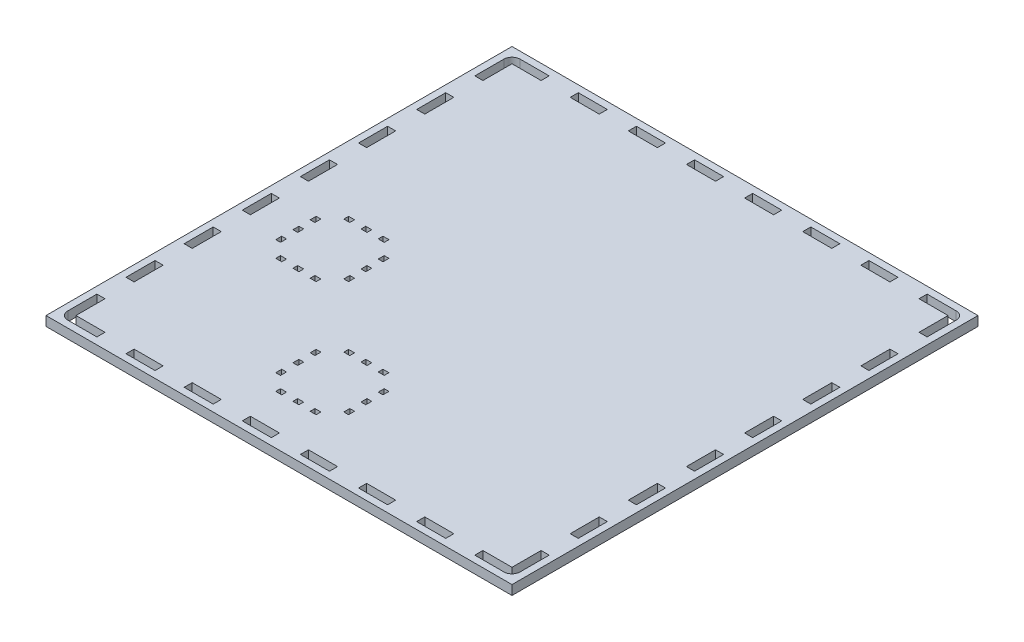
SolidWorks part; units mm, degrees
ref_plane "Front Plane" through (0, 0, 0) normal (0, 0, 1) x (1, 0, 0)
ref_plane "Top Plane" through (0, 0, 0) normal (0, 1, 0) x (1, 0, 0)
ref_plane "Right Plane" through (0, 0, 0) normal (1, 0, 0) x (0, 0, -1)
sketch "Sketch1" plane through (0, 0, 0) normal (0, 1, 0) x (1, 0, 0)
  line L182 (-7.5125, 303.9125) -> (303.8875, 303.9125)
  line L183 (-7.5125, 303.9125) -> (-7.5125, -7.4875)
  line L184 (-7.5125, -7.4875) -> (303.8875, -7.4875)
  line L185 (303.8875, 303.9125) -> (303.8875, -7.4875)
  line L195 (-2.9125, 60.7875) -> (2.4875, 60.7875)
  line L196 (-2.9125, 60.7875) -> (-2.9125, 41.3625)
  line L197 (-2.9125, 41.3625) -> (2.4875, 41.3625)
  line L198 (2.4875, 60.7875) -> (2.4875, 41.3625)
  line L200 (-2.9125, 99.6375) -> (2.4875, 99.6375)
  line L201 (-2.9125, 99.6375) -> (-2.9125, 80.2125)
  line L202 (-2.9125, 80.2125) -> (2.4875, 80.2125)
  line L203 (2.4875, 99.6375) -> (2.4875, 80.2125)
  line L205 (-2.9125, 138.4875) -> (2.4875, 138.4875)
  line L206 (-2.9125, 138.4875) -> (-2.9125, 119.0625)
  line L207 (-2.9125, 119.0625) -> (2.4875, 119.0625)
  line L208 (2.4875, 138.4875) -> (2.4875, 119.0625)
  line L211 (-2.9125, 177.3375) -> (2.4875, 177.3375)
  line L212 (-2.9125, 177.3375) -> (-2.9125, 157.9125)
  line L213 (-2.9125, 157.9125) -> (2.4875, 157.9125)
  line L214 (2.4875, 177.3375) -> (2.4875, 157.9125)
  line L216 (-2.9125, 216.1875) -> (2.4875, 216.1875)
  line L217 (-2.9125, 216.1875) -> (-2.9125, 196.7625)
  line L218 (-2.9125, 196.7625) -> (2.4875, 196.7625)
  line L219 (2.4875, 216.1875) -> (2.4875, 196.7625)
  line L221 (-2.9125, 255.0375) -> (2.4875, 255.0375)
  line L222 (-2.9125, 255.0375) -> (-2.9125, 235.6125)
  line L223 (-2.9125, 235.6125) -> (2.4875, 235.6125)
  line L224 (2.4875, 255.0375) -> (2.4875, 235.6125)
  line L236 (41.3625, 299.3125) -> (60.7875, 299.3125)
  line L237 (41.3625, 299.3125) -> (41.3625, 293.9125)
  line L238 (41.3625, 293.9125) -> (60.7875, 293.9125)
  line L239 (60.7875, 299.3125) -> (60.7875, 293.9125)
  line L241 (80.2125, 299.3125) -> (99.6375, 299.3125)
  line L242 (80.2125, 299.3125) -> (80.2125, 293.9125)
  line L243 (80.2125, 293.9125) -> (99.6375, 293.9125)
  line L244 (99.6375, 299.3125) -> (99.6375, 293.9125)
  line L246 (119.0625, 299.3125) -> (138.4875, 299.3125)
  line L247 (119.0625, 299.3125) -> (119.0625, 293.9125)
  line L248 (119.0625, 293.9125) -> (138.4875, 293.9125)
  line L249 (138.4875, 299.3125) -> (138.4875, 293.9125)
  line L251 (157.9125, 299.3125) -> (177.3375, 299.3125)
  line L252 (157.9125, 299.3125) -> (157.9125, 293.9125)
  line L253 (157.9125, 293.9125) -> (177.3375, 293.9125)
  line L254 (177.3375, 299.3125) -> (177.3375, 293.9125)
  line L256 (196.7625, 299.3125) -> (216.1875, 299.3125)
  line L257 (196.7625, 299.3125) -> (196.7625, 293.9125)
  line L258 (196.7625, 293.9125) -> (216.1875, 293.9125)
  line L259 (216.1875, 299.3125) -> (216.1875, 293.9125)
  line L260 (235.6125, 299.3125) -> (255.0375, 299.3125)
  line L261 (235.6125, 299.3125) -> (235.6125, 293.9125)
  line L262 (235.6125, 293.9125) -> (255.0375, 293.9125)
  line L263 (255.0375, 299.3125) -> (255.0375, 293.9125)
  line L272 (299.2875, 255.0625) -> (293.8875, 255.0625)
  line L273 (299.2875, 255.0625) -> (299.2875, 235.6375)
  line L274 (299.2875, 235.6375) -> (293.8875, 235.6375)
  line L275 (293.8875, 255.0625) -> (293.8875, 235.6375)
  line L276 (299.2875, 216.2125) -> (293.8875, 216.2125)
  line L277 (299.2875, 216.2125) -> (299.2875, 196.7875)
  line L278 (299.2875, 196.7875) -> (293.8875, 196.7875)
  line L279 (293.8875, 216.2125) -> (293.8875, 196.7875)
  line L280 (299.2875, 177.3625) -> (293.8875, 177.3625)
  line L281 (299.2875, 177.3625) -> (299.2875, 157.9375)
  line L282 (299.2875, 157.9375) -> (293.8875, 157.9375)
  line L283 (293.8875, 177.3625) -> (293.8875, 157.9375)
  line L284 (299.2875, 138.5125) -> (293.8875, 138.5125)
  line L285 (299.2875, 138.5125) -> (299.2875, 119.0875)
  line L286 (299.2875, 119.0875) -> (293.8875, 119.0875)
  line L287 (293.8875, 138.5125) -> (293.8875, 119.0875)
  line L288 (299.2875, 99.6625) -> (293.8875, 99.6625)
  line L289 (299.2875, 99.6625) -> (299.2875, 80.2375)
  line L290 (299.2875, 80.2375) -> (293.8875, 80.2375)
  line L291 (293.8875, 99.6625) -> (293.8875, 80.2375)
  line L292 (299.2875, 60.8125) -> (293.8875, 60.8125)
  line L293 (299.2875, 60.8125) -> (299.2875, 41.3875)
  line L294 (299.2875, 41.3875) -> (293.8875, 41.3875)
  line L295 (293.8875, 60.8125) -> (293.8875, 41.3875)
  line L304 (255.0125, 2.5125) -> (235.5875, 2.5125)
  line L305 (255.0125, 2.5125) -> (255.0125, -2.8875)
  line L306 (255.0125, -2.8875) -> (235.5875, -2.8875)
  line L307 (235.5875, 2.5125) -> (235.5875, -2.8875)
  line L308 (216.1625, 2.5125) -> (196.7375, 2.5125)
  line L309 (216.1625, 2.5125) -> (216.1625, -2.8875)
  line L310 (216.1625, -2.8875) -> (196.7375, -2.8875)
  line L311 (196.7375, 2.5125) -> (196.7375, -2.8875)
  line L312 (177.3125, 2.5125) -> (157.8875, 2.5125)
  line L313 (177.3125, 2.5125) -> (177.3125, -2.8875)
  line L314 (177.3125, -2.8875) -> (157.8875, -2.8875)
  line L315 (157.8875, 2.5125) -> (157.8875, -2.8875)
  line L316 (138.4625, 2.5125) -> (119.0375, 2.5125)
  line L317 (138.4625, 2.5125) -> (138.4625, -2.8875)
  line L318 (138.4625, -2.8875) -> (119.0375, -2.8875)
  line L319 (119.0375, 2.5125) -> (119.0375, -2.8875)
  line L320 (99.6125, 2.5125) -> (80.1875, 2.5125)
  line L321 (99.6125, 2.5125) -> (99.6125, -2.8875)
  line L322 (99.6125, -2.8875) -> (80.1875, -2.8875)
  line L323 (80.1875, 2.5125) -> (80.1875, -2.8875)
  line L324 (60.7625, 2.5125) -> (41.3375, 2.5125)
  line L325 (60.7625, 2.5125) -> (60.7625, -2.8875)
  line L326 (60.7625, -2.8875) -> (41.3375, -2.8875)
  line L327 (41.3375, 2.5125) -> (41.3375, -2.8875)
  line L528 (36.1625, 151.0125) -> (40.1625, 151.0125)
  line L529 (36.1625, 151.0125) -> (36.1625, 147.8375)
  line L530 (36.1625, 147.8375) -> (40.1625, 147.8375)
  line L531 (40.1625, 151.0125) -> (40.1625, 147.8375)
  line L532 (47.6625, 151.0125) -> (51.6625, 151.0125)
  line L533 (47.6625, 151.0125) -> (47.6625, 147.8375)
  line L534 (47.6625, 147.8375) -> (51.6625, 147.8375)
  line L535 (51.6625, 151.0125) -> (51.6625, 147.8375)
  line L536 (59.1625, 151.0125) -> (63.1625, 151.0125)
  line L537 (59.1625, 151.0125) -> (59.1625, 147.8375)
  line L538 (59.1625, 147.8375) -> (63.1625, 147.8375)
  line L539 (63.1625, 151.0125) -> (63.1625, 147.8375)
  line L540 (70.8125, 140.1875) -> (73.9875, 140.1875)
  line L541 (70.8125, 140.1875) -> (70.8125, 136.1875)
  line L542 (70.8125, 136.1875) -> (73.9875, 136.1875)
  line L543 (73.9875, 140.1875) -> (73.9875, 136.1875)
  line L544 (70.8125, 128.6875) -> (73.9875, 128.6875)
  line L545 (70.8125, 128.6875) -> (70.8125, 124.6875)
  line L546 (70.8125, 124.6875) -> (73.9875, 124.6875)
  line L547 (73.9875, 128.6875) -> (73.9875, 124.6875)
  line L548 (70.8125, 117.1875) -> (73.9875, 117.1875)
  line L549 (70.8125, 117.1875) -> (70.8125, 113.1875)
  line L550 (70.8125, 113.1875) -> (73.9875, 113.1875)
  line L551 (73.9875, 117.1875) -> (73.9875, 113.1875)
  line L552 (63.1625, 105.5375) -> (59.1625, 105.5375)
  line L553 (63.1625, 105.5375) -> (63.1625, 102.3625)
  line L554 (63.1625, 102.3625) -> (59.1625, 102.3625)
  line L555 (59.1625, 105.5375) -> (59.1625, 102.3625)
  line L556 (51.6625, 105.5375) -> (47.6625, 105.5375)
  line L557 (51.6625, 105.5375) -> (51.6625, 102.3625)
  line L558 (51.6625, 102.3625) -> (47.6625, 102.3625)
  line L559 (47.6625, 105.5375) -> (47.6625, 102.3625)
  line L560 (40.1625, 105.5375) -> (36.1625, 105.5375)
  line L561 (40.1625, 105.5375) -> (40.1625, 102.3625)
  line L562 (40.1625, 102.3625) -> (36.1625, 102.3625)
  line L563 (36.1625, 105.5375) -> (36.1625, 102.3625)
  line L564 (28.5125, 113.1875) -> (25.3375, 113.1875)
  line L565 (28.5125, 113.1875) -> (28.5125, 117.1875)
  line L566 (28.5125, 117.1875) -> (25.3375, 117.1875)
  line L567 (25.3375, 113.1875) -> (25.3375, 117.1875)
  line L568 (28.5125, 124.6875) -> (25.3375, 124.6875)
  line L569 (28.5125, 124.6875) -> (28.5125, 128.6875)
  line L570 (28.5125, 128.6875) -> (25.3375, 128.6875)
  line L571 (25.3375, 124.6875) -> (25.3375, 128.6875)
  line L572 (28.5125, 136.1875) -> (25.3375, 136.1875)
  line L573 (28.5125, 136.1875) -> (28.5125, 140.1875)
  line L574 (28.5125, 140.1875) -> (25.3375, 140.1875)
  line L575 (25.3375, 136.1875) -> (25.3375, 140.1875)
  line L576 (113.1625, 74.0125) -> (117.1625, 74.0125)
  line L577 (113.1625, 74.0125) -> (113.1625, 70.8375)
  line L578 (113.1625, 70.8375) -> (117.1625, 70.8375)
  line L579 (117.1625, 74.0125) -> (117.1625, 70.8375)
  line L580 (124.6625, 74.0125) -> (128.6625, 74.0125)
  line L581 (124.6625, 74.0125) -> (124.6625, 70.8375)
  line L582 (124.6625, 70.8375) -> (128.6625, 70.8375)
  line L583 (128.6625, 74.0125) -> (128.6625, 70.8375)
  line L584 (136.1625, 74.0125) -> (140.1625, 74.0125)
  line L585 (136.1625, 74.0125) -> (136.1625, 70.8375)
  line L586 (136.1625, 70.8375) -> (140.1625, 70.8375)
  line L587 (140.1625, 74.0125) -> (140.1625, 70.8375)
  line L588 (150.9875, 63.1875) -> (147.8125, 63.1875)
  line L589 (150.9875, 63.1875) -> (150.9875, 59.1875)
  line L590 (150.9875, 59.1875) -> (147.8125, 59.1875)
  line L591 (147.8125, 63.1875) -> (147.8125, 59.1875)
  line L592 (150.9875, 51.6875) -> (147.8125, 51.6875)
  line L593 (150.9875, 51.6875) -> (150.9875, 47.6875)
  line L594 (150.9875, 47.6875) -> (147.8125, 47.6875)
  line L595 (147.8125, 51.6875) -> (147.8125, 47.6875)
  line L596 (150.9875, 40.1875) -> (147.8125, 40.1875)
  line L597 (150.9875, 40.1875) -> (150.9875, 36.1875)
  line L598 (150.9875, 36.1875) -> (147.8125, 36.1875)
  line L599 (147.8125, 40.1875) -> (147.8125, 36.1875)
  line L600 (140.1625, 28.5375) -> (136.1625, 28.5375)
  line L601 (140.1625, 28.5375) -> (140.1625, 25.3625)
  line L602 (140.1625, 25.3625) -> (136.1625, 25.3625)
  line L603 (136.1625, 28.5375) -> (136.1625, 25.3625)
  line L604 (128.6625, 28.5375) -> (124.6625, 28.5375)
  line L605 (128.6625, 28.5375) -> (128.6625, 25.3625)
  line L606 (128.6625, 25.3625) -> (124.6625, 25.3625)
  line L607 (124.6625, 28.5375) -> (124.6625, 25.3625)
  line L608 (117.1625, 28.5375) -> (113.1625, 28.5375)
  line L609 (117.1625, 28.5375) -> (117.1625, 25.3625)
  line L610 (117.1625, 25.3625) -> (113.1625, 25.3625)
  line L611 (113.1625, 28.5375) -> (113.1625, 25.3625)
  line L612 (105.5125, 36.1875) -> (102.3375, 36.1875)
  line L613 (105.5125, 36.1875) -> (105.5125, 40.1875)
  line L614 (105.5125, 40.1875) -> (102.3375, 40.1875)
  line L615 (102.3375, 36.1875) -> (102.3375, 40.1875)
  line L616 (105.5125, 47.6875) -> (102.3375, 47.6875)
  line L617 (105.5125, 47.6875) -> (105.5125, 51.6875)
  line L618 (105.5125, 51.6875) -> (102.3375, 51.6875)
  line L619 (102.3375, 47.6875) -> (102.3375, 51.6875)
  line L620 (105.5125, 59.1875) -> (102.3375, 59.1875)
  line L621 (105.5125, 59.1875) -> (105.5125, 63.1875)
  line L622 (105.5125, 63.1875) -> (102.3375, 63.1875)
  line L623 (102.3375, 59.1875) -> (102.3375, 63.1875)
  dimension "D1" = 311.4
  dimension "D3" = 311.4
extrude "Boss-Extrude4" add sketch "Sketch1" along normal blind 6.35
sketch "Sketch4" plane through (0, 6.35, 0) normal (0, 1, 0) x (1, 0, 0)
  line L0 (303.8875, 303.9125) -> (-7.5125, 303.9125) construction
  line B0 (41.3375, 2.5125) -> (60.7625, 2.5125)
  line B1 (2.4875, 2.5125) -> (21.9125, 2.5125)
  line B2 (2.4875, 2.5125) -> (2.4875, -2.8875)
  line B3 (2.4875, -2.8875) -> (21.9125, -2.8875)
  line B4 (21.9125, 2.5125) -> (21.9125, -2.8875)
  line B5 (41.3375, 2.5125) -> (41.3375, -2.8875)
  line B6 (41.3375, -2.8875) -> (60.7625, -2.8875)
  line B7 (60.7625, 2.5125) -> (60.7625, -2.8875)
  line B8 (80.1875, 2.5125) -> (99.6125, 2.5125)
  line B9 (80.1875, 2.5125) -> (80.1875, -2.8875)
  line B10 (80.1875, -2.8875) -> (99.6125, -2.8875)
  line B11 (99.6125, 2.5125) -> (99.6125, -2.8875)
  line B12 (119.0375, 2.5125) -> (138.4625, 2.5125)
  line B13 (119.0375, 2.5125) -> (119.0375, -2.8875)
  line B14 (119.0375, -2.8875) -> (138.4625, -2.8875)
  line B15 (138.4625, 2.5125) -> (138.4625, -2.8875)
  line B16 (157.8875, 2.5125) -> (177.3125, 2.5125)
  line B17 (157.8875, 2.5125) -> (157.8875, -2.8875)
  line B18 (157.8875, -2.8875) -> (177.3125, -2.8875)
  line B19 (177.3125, 2.5125) -> (177.3125, -2.8875)
  line B20 (196.7375, 2.5125) -> (216.1625, 2.5125)
  line B21 (196.7375, 2.5125) -> (196.7375, -2.8875)
  line B22 (196.7375, -2.8875) -> (216.1625, -2.8875)
  line B23 (216.1625, 2.5125) -> (216.1625, -2.8875)
  line B24 (235.5875, 2.5125) -> (255.0125, 2.5125)
  line B25 (235.5875, 2.5125) -> (235.5875, -2.8875)
  line B26 (235.5875, -2.8875) -> (255.0125, -2.8875)
  line B27 (255.0125, 2.5125) -> (255.0125, -2.8875)
  line B28 (274.4375, 2.5125) -> (293.8625, 2.5125)
  line B29 (274.4375, 2.5125) -> (274.4375, -2.8875)
  line B30 (274.4375, -2.8875) -> (293.8625, -2.8875)
  line B31 (293.8625, 2.5125) -> (293.8625, -2.8875)
  line B32 (-2.9125, 60.7875) -> (2.4875, 60.7875)
  line B33 (-2.9125, 2.5125) -> (2.4875, 2.5125)
  line B34 (-2.9125, 2.5125) -> (-2.9125, 21.9375)
  line B35 (-2.9125, 21.9375) -> (2.4875, 21.9375)
  line B36 (2.4875, 2.5125) -> (2.4875, 21.9375)
  line B37 (2.4875, 41.3625) -> (2.4875, 60.7875)
  line B38 (-2.9125, 41.3625) -> (-2.9125, 60.7875)
  line B39 (-2.9125, 41.3625) -> (2.4875, 41.3625)
  line B40 (-2.9125, 99.6375) -> (2.4875, 99.6375)
  line B41 (2.4875, 80.2125) -> (2.4875, 99.6375)
  line B42 (-2.9125, 80.2125) -> (-2.9125, 99.6375)
  line B43 (-2.9125, 80.2125) -> (2.4875, 80.2125)
  line B44 (-2.9125, 138.4875) -> (2.4875, 138.4875)
  line B45 (2.4875, 119.0625) -> (2.4875, 138.4875)
  line B46 (-2.9125, 119.0625) -> (-2.9125, 138.4875)
  line B47 (-2.9125, 119.0625) -> (2.4875, 119.0625)
  line B48 (-2.9125, 177.3375) -> (2.4875, 177.3375)
  line B49 (2.4875, 157.9125) -> (2.4875, 177.3375)
  line B50 (-2.9125, 157.9125) -> (-2.9125, 177.3375)
  line B51 (-2.9125, 157.9125) -> (2.4875, 157.9125)
  line B52 (-2.9125, 216.1875) -> (2.4875, 216.1875)
  line B53 (2.4875, 196.7625) -> (2.4875, 216.1875)
  line B54 (-2.9125, 196.7625) -> (-2.9125, 216.1875)
  line B55 (-2.9125, 196.7625) -> (2.4875, 196.7625)
  line B56 (-2.9125, 255.0375) -> (2.4875, 255.0375)
  line B57 (2.4875, 235.6125) -> (2.4875, 255.0375)
  line B58 (-2.9125, 235.6125) -> (-2.9125, 255.0375)
  line B59 (-2.9125, 235.6125) -> (2.4875, 235.6125)
  line B60 (-2.9125, 293.8875) -> (2.4875, 293.8875)
  line B61 (2.4875, 274.4625) -> (2.4875, 293.8875)
  line B62 (-2.9125, 274.4625) -> (-2.9125, 293.8875)
  line B63 (-2.9125, 274.4625) -> (2.4875, 274.4625)
  line B64 (-7.5125, 303.9125) -> (303.8875, -7.4875) construction
  line B65 (21.9375, 299.3125) -> (21.9375, 293.9125)
  line B66 (21.9375, 299.3125) -> (2.5125, 299.3125)
  line B67 (21.9375, 293.9125) -> (2.5125, 293.9125)
  line B68 (2.5125, 299.3125) -> (2.5125, 293.9125)
  line B69 (60.7875, 299.3125) -> (60.7875, 293.9125)
  line B70 (60.7875, 299.3125) -> (41.3625, 299.3125)
  line B71 (60.7875, 293.9125) -> (41.3625, 293.9125)
  line B72 (41.3625, 299.3125) -> (41.3625, 293.9125)
  line B73 (99.6375, 299.3125) -> (99.6375, 293.9125)
  line B74 (99.6375, 299.3125) -> (80.2125, 299.3125)
  line B75 (99.6375, 293.9125) -> (80.2125, 293.9125)
  line B76 (80.2125, 299.3125) -> (80.2125, 293.9125)
  line B77 (138.4875, 299.3125) -> (138.4875, 293.9125)
  line B78 (138.4875, 299.3125) -> (119.0625, 299.3125)
  line B79 (138.4875, 293.9125) -> (119.0625, 293.9125)
  line B80 (119.0625, 299.3125) -> (119.0625, 293.9125)
  line B81 (177.3375, 299.3125) -> (177.3375, 293.9125)
  line B82 (177.3375, 299.3125) -> (157.9125, 299.3125)
  line B83 (177.3375, 293.9125) -> (157.9125, 293.9125)
  line B84 (157.9125, 299.3125) -> (157.9125, 293.9125)
  line B85 (216.1875, 299.3125) -> (216.1875, 293.9125)
  line B86 (216.1875, 299.3125) -> (196.7625, 299.3125)
  line B87 (216.1875, 293.9125) -> (196.7625, 293.9125)
  line B88 (196.7625, 299.3125) -> (196.7625, 293.9125)
  line B89 (255.0375, 299.3125) -> (255.0375, 293.9125)
  line B90 (255.0375, 299.3125) -> (235.6125, 299.3125)
  line B91 (255.0375, 293.9125) -> (235.6125, 293.9125)
  line B92 (293.8875, 293.9125) -> (274.4625, 293.9125)
  line B93 (274.4625, 299.3125) -> (274.4625, 293.9125)
  line B94 (293.8875, 299.3125) -> (274.4625, 299.3125)
  line B95 (293.8875, 299.3125) -> (293.8875, 293.9125)
  line B96 (235.6125, 299.3125) -> (235.6125, 293.9125)
  line B97 (293.8875, 2.5375) -> (299.2875, 2.5375)
  line B98 (299.2875, 21.9625) -> (299.2875, 2.5375)
  line B99 (293.8875, 21.9625) -> (299.2875, 21.9625)
  line B100 (293.8875, 21.9625) -> (293.8875, 2.5375)
  line B101 (293.8875, 41.3875) -> (299.2875, 41.3875)
  line B102 (299.2875, 60.8125) -> (299.2875, 41.3875)
  line B103 (293.8875, 60.8125) -> (299.2875, 60.8125)
  line B104 (293.8875, 60.8125) -> (293.8875, 41.3875)
  line B105 (293.8875, 80.2375) -> (299.2875, 80.2375)
  line B106 (299.2875, 99.6625) -> (299.2875, 80.2375)
  line B107 (293.8875, 99.6625) -> (299.2875, 99.6625)
  line B108 (293.8875, 99.6625) -> (293.8875, 80.2375)
  line B109 (293.8875, 119.0875) -> (299.2875, 119.0875)
  line B110 (299.2875, 138.5125) -> (299.2875, 119.0875)
  line B111 (293.8875, 138.5125) -> (299.2875, 138.5125)
  line B112 (293.8875, 138.5125) -> (293.8875, 119.0875)
  line B113 (293.8875, 157.9375) -> (299.2875, 157.9375)
  line B114 (299.2875, 177.3625) -> (299.2875, 157.9375)
  line B115 (293.8875, 177.3625) -> (299.2875, 177.3625)
  line B116 (293.8875, 177.3625) -> (293.8875, 157.9375)
  line B117 (293.8875, 196.7875) -> (299.2875, 196.7875)
  line B118 (299.2875, 216.2125) -> (299.2875, 196.7875)
  line B119 (293.8875, 216.2125) -> (299.2875, 216.2125)
  line B120 (293.8875, 216.2125) -> (293.8875, 196.7875)
  line B121 (293.8875, 235.6375) -> (299.2875, 235.6375)
  line B122 (299.2875, 255.0625) -> (299.2875, 235.6375)
  line B123 (293.8875, 255.0625) -> (299.2875, 255.0625)
  line B124 (293.8875, 274.4875) -> (299.2875, 274.4875)
  line B125 (299.2875, 293.9125) -> (299.2875, 274.4875)
  line B126 (293.8875, 293.9125) -> (299.2875, 293.9125)
  line B127 (293.8875, 293.9125) -> (293.8875, 274.4875)
  line B128 (293.8875, 255.0625) -> (293.8875, 235.6375)
  line B129 (2.5125, 293.9125) -> (2.4875, 293.8875)
  line B130 (293.8875, 2.5375) -> (293.8625, 2.5125)
  line B131 (35.6625, 260.7375) -> (115.6625, 260.7375)
  line B132 (35.6625, 260.7375) -> (35.6625, 180.7375)
  line B133 (35.6625, 180.7375) -> (115.6625, 180.7375)
  line B134 (115.6625, 260.7375) -> (115.6625, 180.7375)
  arc B135 (-2.9125, 293.8875) -> (2.5125, 299.2874) centre (2.4875, 293.8875) cw
  arc B136 (293.8625, -2.8875) -> (299.2624, 2.5375) centre (293.8625, 2.5125) ccw
  arc B137 (299.2875, 293.9125) -> (293.8875, 299.3125) centre (293.8875, 293.9125) ccw
  arc B138 (2.4875, -2.8875) -> (-2.9125, 2.5125) centre (2.4875, 2.5125) cw
sketch_block_instance "Outer Mounting Holes-4"
sketch_block "Outer Mounting Holes" parameters "D1"=5.4, "D2"=19.425, "D3"=19.425, "D4"=19.425, "D5"=80, "D6"=302.2
extrude "Cut-Extrude3" cut sketch "Sketch4" against normal blind 6.35 contours B66 B68 B67 B65 | B62 B63 B61 B60 | B135 B60 B129 B68 | B126 B137 B95 | B95 B94 B93 B92 | B126 B127 B124 B125 | B33 B36 B35 B34 | B4 B1 B2 B3 | B138 B2 B33 | B31 B136 B97 B130 | B31 B28 B29 B30 | B99 B100 B97 B98
equation "\"stepper width\"=4.23"
equation "\"stepper hole disctance\"= 3.1"
equation "\"stepper hole diameter\"=0.34"
equation "\"stepper shaft hole\"=2.4"
equation "\"tooth width\"=0.4"
equation "\"tooth thickness\"=0.3175"
equation "\"tooth to side\"=0.75"
equation "\"motor chamber height\"= 6"
equation "\"enclosure length\"= 22 + 6"
equation "\"platform diameter\"= 9"
equation "\"teeth width\"=0.3175"
equation "\"teeth lenght\"=2"
equation "\"tower width\"=7.7"
equation "\"support width\"=1"
equation "\"trial hole spacing\"= 0.75"
equation "\"mounting distance\"= 4"
equation "\"half belt distance\"=5.5"
equation "\"holder distance to wall\"= 2.25"
equation "\"bearing outer diameter\"= 1.6"
equation "\"half belt length\"=5.5"
equation "\"screw hole diameter\"=0.351"
equation "\"distance between screw hles\"=3"
equation "\"spinner to stack center to center\"= 15"
equation "\"stack to elevator center to center\"=20"
equation "\"elevator to wall\"=3.5"
equation "\"D1\"= \"tooth width\""
equation "\"D2\"= \"tooth thickness\""
equation "\"D3\"= \"tooth to side\""
equation "\"D2@Elevator Platform Block\"=\"motor width\""
equation "\"D31@Sketch1\"=\"teeth lenght\""
equation "\"D32@Sketch1\"=\"tooth thickness\""
equation "\"D1\" = \"tooth width\""
equation "\"D2\" = \"tooth thickness\""
equation "\"D3\" = \"tooth to side\""
equation "\"D4\" = \"tooth to side\""
equation "\"D14@Sketch1\"=\"holder distance to wall\""
equation "\"D5@Sketch1\"=\"teeth lenght\""
equation "\"D2@Sketch1\"=\"teeth width\""
equation "\"D15@Sketch1\"=\"stack to elevator center to center\""
equation "\"D1\" = \"tooth thickness\""
equation "\"D12@Sketch1\"=\"stack to elevator center to center\"/2"
equation "\"D11@Sketch1\"=\"spinner to stack center to center\"/2"
equation "\"D10@Sketch1\"=\"holder distance to wall\""
equation "\"D13@Sketch1\"=\"spinner to stack center to center\""
equation "\"D1\" = \"motor width\""
equation "\"D1\" = \"elevator width\""
equation "\"D3\" = \"drivign screw diameter\""
equation "\"D3\" = \"motor width\""
equation "\"D2\" = \"elevator width\""
equation "\"D2\" = \"motor width\""
equation "\"D10@Sketch1\"=\"elevator to wall\""
equation "\"D11@Sketch1\"=\"elevator to wall\""
